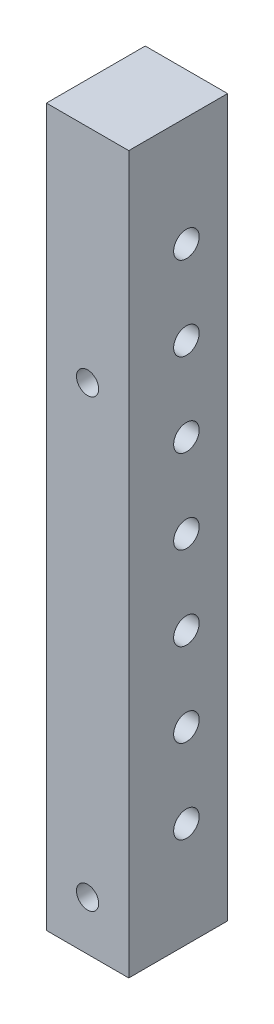
SolidWorks part; units mm, degrees
ref_plane "前基準面" through (0, 0, 0) normal (0, 0, 1) x (1, 0, 0)
ref_plane "上基準面" through (0, 0, 0) normal (0, 1, 0) x (1, 0, 0)
ref_plane "右基準面" through (0, 0, 0) normal (1, 0, 0) x (0, 0, -1)
ref_plane "平面1" through (5, 0, 0) normal (1, 0, 0) x (0, 0, -1)
sketch "草圖1" plane through (5, 0, 0) normal (1, 0, 0) x (0, 0, -1)
  line L0 (-6, 0) -> (6, 0)
  line L1 (6, 0) -> (6, 87)
  line L2 (6, 87) -> (-6, 87)
  line L3 (-6, 87) -> (-6, 0)
extrude "填料-伸長1" add sketch "草圖1" against normal blind 10
hole_wizard "Ø3.1 (3.1) 直徑孔1" positions "草圖3" profile "草圖2" hole size "Ø3.1" standard "Ansi Metric"
sketch "草圖3" plane through (5, 0, 0) normal (1, 0, 0) x (0, 0, -1)
  point P0 (1, 63.53)
  point P1 (1, 43.21)
  point P2 (1, 22.89)
  point P3 (1, 53.37)
  point P4 (1, 33.05)
  point P5 (1, 12.73)
  point P6 (1, 73.69)
sketch "草圖2" plane through (5, 63.53, -1) normal (0, 1, 0) x (0, 0, -1)
  line L0 (0, 0) -> (0, 10)
  line L1 (0, 10) -> (1.55, 10)
  line L2 (1.55, 10) -> (1.55, 0)
  line L5 (1.55, 0) -> (0, 0)
  line L11 (0, -6.35) -> (0, 107.95) construction
  dimension "砮 ふ 畖" = 3.1
  dimension "砮 ふ瞏 " = 10
hole_wizard "Ø2.7 (2.7) 直徑孔1" positions "草圖5" profile "草圖4" hole size "Ø2.7" standard "Ansi Metric"
sketch "草圖5" plane through (0, 0, 6) normal (0, 0, 1) x (1, 0, 0)
  point P0 (0, 60.1)
  point P1 (0, 6)
sketch "草圖4" plane through (0, 60.1, 6) normal (1, 0, 0) x (0, -1, 0)
  line L0 (0, 0) -> (0, 12)
  line L1 (0, 12) -> (1.35, 12)
  line L2 (1.35, 12) -> (1.35, 0)
  line L5 (1.35, 0) -> (0, 0)
  line L11 (0, -6.35) -> (0, 107.95) construction
  dimension "砮 ふ 畖" = 2.7
  dimension "砮 ふ瞏 " = 12
